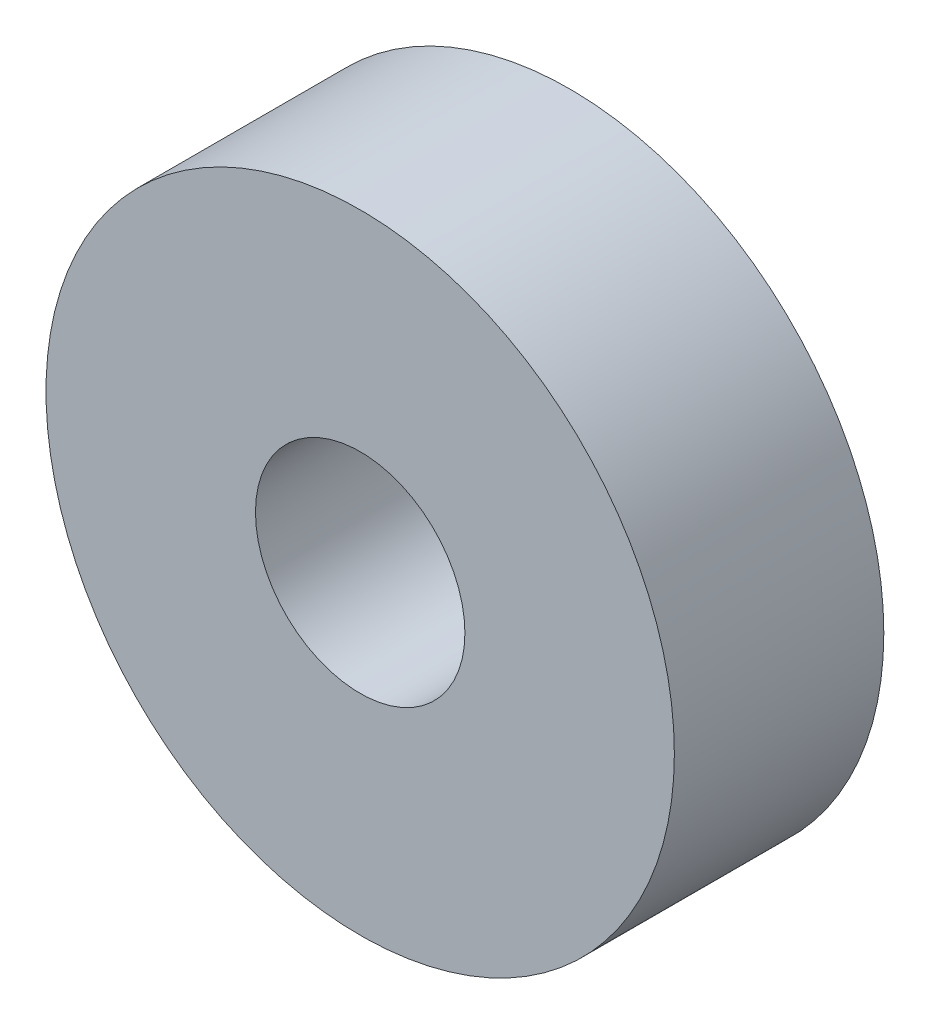
SolidWorks part; units mm, degrees
ref_plane "Front Plane" through (0, 0, 0) normal (0, 0, 1) x (1, 0, 0)
ref_plane "Top Plane" through (0, 0, 0) normal (0, 1, 0) x (1, 0, 0)
ref_plane "Right Plane" through (0, 0, 0) normal (1, 0, 0) x (0, 0, -1)
sketch "Sketch1" plane through (0, 0, 0) normal (0, 0, 1) x (1, 0, 0)
  circle A0 centre (0, 0) radius 20
  circle A1 centre (0, 0) radius 60
  dimension "D1" = 40
  dimension "D2" = 120
extrude "Boss-Extrude1" add sketch "Sketch1" along normal mid plane 40
